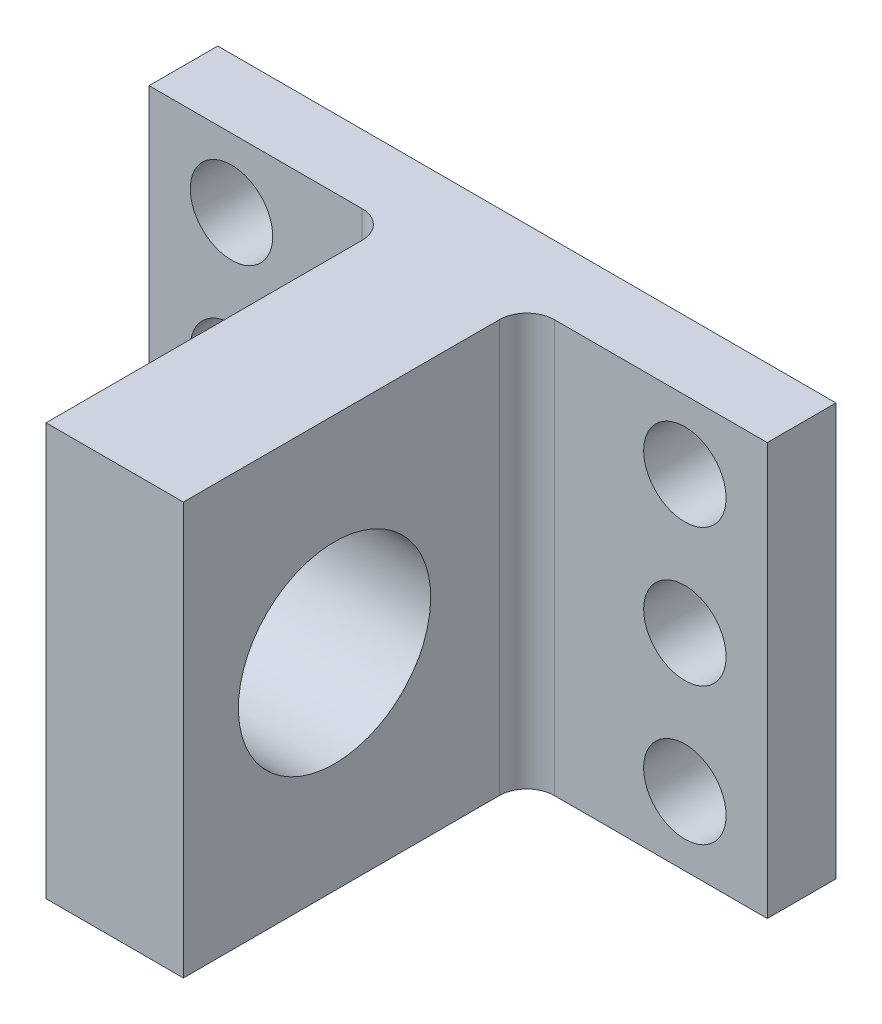
SolidWorks part; units mm, degrees
ref_plane "Piano frontale" through (0, 0, 0) normal (0, 0, 1) x (1, 0, 0)
ref_plane "Piano superiore" through (0, 0, 0) normal (0, 1, 0) x (1, 0, 0)
ref_plane "Piano destro" through (0, 0, 0) normal (1, 0, 0) x (0, 0, -1)
sketch "Sketch1" plane through (0, 0, 0) normal (0, 0, 1) x (1, 0, 0)
  line L0 (-22.5, 15) -> (22.5, -15) construction
  line L1 (-22.5, 15) -> (22.5, 15)
  line L2 (-22.5, 15) -> (-22.5, -15)
  line L3 (-22.5, -15) -> (22.5, -15)
  line L4 (22.5, 15) -> (22.5, -15)
  line L5 (-22.5, -15) -> (22.5, 15) construction
  point P4 (0, 0)
  dimension "D1" = 30
  dimension "D2" = 45
extrude "Base" add sketch "Sketch1" along normal blind 5
sketch "Sketch2" plane through (0, 0, 5) normal (0, 0, 1) x (1, 0, 0)
  line L0 (-5, 15) -> (5, -15) construction
  line L1 (-5, 15) -> (5, 15)
  line L2 (-5, 15) -> (-5, -15)
  line L3 (-5, -15) -> (5, -15)
  line L4 (5, 15) -> (5, -15)
  line L5 (-5, -15) -> (5, 15) construction
  line L6 (22.5, 0) -> (-22.5, 0) construction
  line L7 (22.5, -15) -> (22.5, 15) construction
  line L8 (-22.5, 15) -> (-22.5, -15) construction
  point P10 (0, 0)
  point P11 (0, 0)
  dimension "D1" = 30
  dimension "D2" = 10
extrude "Boss-Extrude2" add sketch "Sketch2" along normal blind 25
sketch "Sketch3" plane through (-5, 0, 0) normal (-1, 0, 0) x (0, 0, 1)
  line L0 (30, 15) -> (30, -15) construction
  line L1 (30, 15) -> (5, 15) construction
  circle A0 centre (19, 0) radius 7
  dimension "D1" = 14
  dimension "D2" = 11
  dimension "D3" = 15
extrude "Cut-Extrude3" cut sketch "Sketch3" against normal blind 10
sketch "Sketch9" plane through (0, 0, 5) normal (0, 0, 1) x (1, 0, 0)
  line L0 (-16.5, 15) -> (-16.5, -15) construction
  line L2 (-22.5, 0) -> (22.5, 0) construction
  line L3 (-22.5, 15) -> (-22.5, -15) construction
  line L4 (22.5, -15) -> (22.5, 15) construction
  line L5 (0, 15) -> (0, -15) construction
  line L6 (22.5, 15) -> (5, 15) construction
  line L7 (-22.5, -15) -> (-5, -15) construction
  circle A1 centre (-16.5, 10) radius 3
  circle A7 centre (-16.5, 0) radius 3
  circle A8 centre (-16.5, -10) radius 3
  circle A9 centre (16.5, -10) radius 3
  circle A10 centre (16.5, 0) radius 3
  circle A11 centre (16.5, 10) radius 3
  point P2 (-13.75, 15)
  point P3 (-13.75, 15)
  point P6 (0, 0)
  dimension "D1" = 5
  dimension "D2" = 6
  dimension "D3" = 6
extrude "Screw" cut sketch "Sketch9" against normal blind 5
fillet "Fillet1" radius 2 1 edges at (-5, 0, 5)
fillet "Fillet2" radius 2 1 edges at (5, 0, 5)
